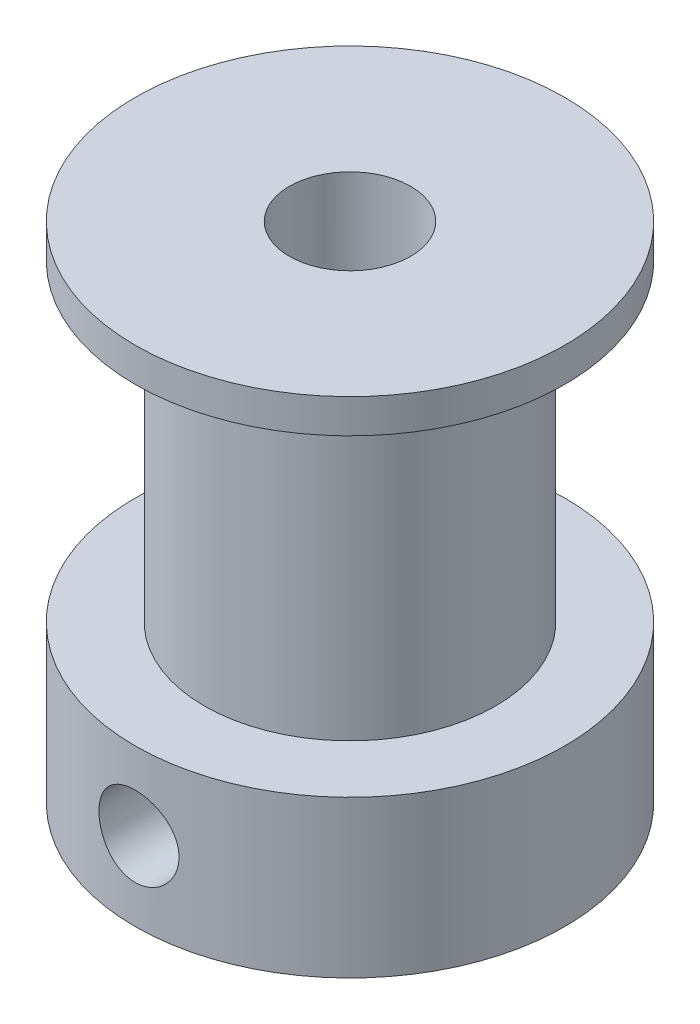
SolidWorks part; units mm, degrees
material "aluminio"
ref_plane "Alzado" through (0, 0, 0) normal (0, 0, 1) x (1, 0, 0)
ref_plane "Planta" through (0, 0, 0) normal (0, 1, 0) x (1, 0, 0)
ref_plane "Vista lateral" through (0, 0, 0) normal (1, 0, 0) x (0, 0, -1)
sketch "Croquis1" plane through (0, 0, 0) normal (0, 0, 1) x (1, 0, 0)
  line L0 (0, 0) -> (0, 36.7556) construction
  line L2 (8.85, 6.45) -> (8.85, 0)
  line L3 (2.5, 20.75) -> (8.85, 20.75)
  line L4 (8.85, 20.75) -> (8.85, 19.35)
  line L5 (8.85, 19.35) -> (6, 19.35)
  line L6 (6, 19.35) -> (6, 6.45)
  line L7 (6, 6.45) -> (8.85, 6.45)
  line L9 (8.85, 0) -> (2.5, 0)
  line L10 (2.5, 0) -> (2.5, 20.75)
  dimension "D1" = 1.4
  dimension "D2" = 6.45
  dimension "D4" = 5
  dimension "D5" = 12
  dimension "D6" = 17.7
  dimension "D11" = 12.9
revolve "Revolución1" add sketch "Croquis1" angle 360 about L0
hole_wizard "Taladro roscado M41" positions "Croquis4" profile "Croquis3" tap size "M4" standard "ISO"
sketch "Croquis4" plane through (0, 0, 0) normal (0, 0, 1) x (1, 0, 0)
  line L1 (0, 0) -> (0, 6.45) construction
  line L2 (8.85, 6.45) -> (-8.85, 6.45) construction
  point P2 (0, 3.225)
sketch "Croquis3" plane through (0, 3.225, 0) normal (1, 0, 0) x (0, 1, 0)
  line L0 (0, 0) -> (0, 8.851)
  line L1 (0, 8.851) -> (1.65, 8.851)
  line L2 (1.65, 8.851) -> (1.65, 0)
  line L5 (1.65, 0) -> (0, 0)
  line L11 (0, -6.35) -> (0, 107.95) construction
  dimension "Diámetro de perforador para roscar hasta el siguiente" = 3.3
  dimension "Profundidad de perforador para roscar hasta el siguiente" = 8.851
cosmetic thread "Rosca de taladro3" parameters "D2"=4
cosmetic thread "Rosca cosmética2" parameters "D2"=4
pattern_circular "MatrizC1" count 2 over 90 about axis through (0, 0, 0) along (0, -1, 0) of "Taladro roscado M41"
cosmetic thread "Rosca cosmética1" parameters "D2"=4
